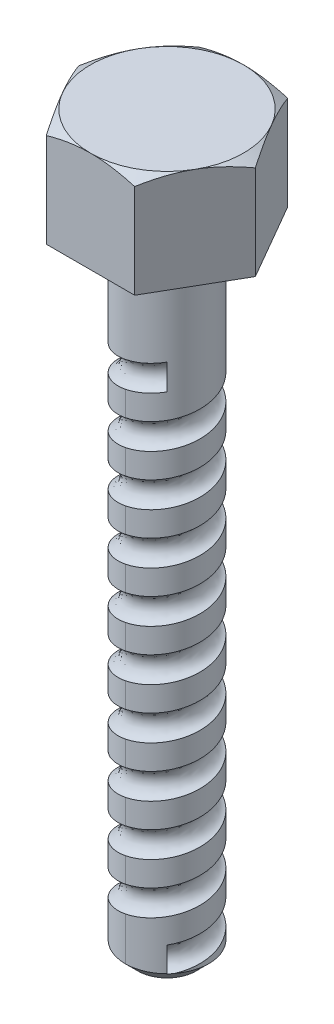
SolidWorks part; units mm, degrees
material "201 Annealed Stainless Steel (SS)"
ref_plane "Front Plane" through (0, 0, 0) normal (0, 0, 1) x (1, 0, 0)
ref_plane "Top Plane" through (0, 0, 0) normal (0, 1, 0) x (1, 0, 0)
ref_plane "Right Plane" through (0, 0, 0) normal (1, 0, 0) x (0, 0, -1)
sketch "Sketch1" plane through (0, 0, 0) normal (0, 1, 0) x (1, 0, 0)
  line L1 (-7, 0) -> (-3.5, -6.0622)
  line L2 (-3.5, -6.0622) -> (3.5, -6.0622)
  line L3 (3.5, -6.0622) -> (7, 0)
  line L4 (7, 0) -> (3.5, 6.0622)
  line L5 (3.5, 6.0622) -> (-3.5, 6.0622)
  line L6 (-3.5, 6.0622) -> (-7, 0)
  circle A0 centre (0, 0) radius 6.0622 construction
  dimension "D1" = 14
extrude "Boss-Extrude1" add sketch "Sketch1" along normal blind 8
sketch "Sketch2" plane through (0, 8, 0) normal (0, 1, 0) x (1, 0, 0)
  line L0 (3.5, 6.0622) -> (-3.5, 6.0622) construction
  circle A0 centre (0, 0) radius 6.0622
extrude "Cut-Extrude2" cut sketch "Sketch2" against normal blind 8 draft 60 flip side to cut
sketch "Sketch3" plane through (0, 0, 0) normal (0, -1, 0) x (1, 0, 0)
  circle A0 centre (0, 0) radius 3.3
  dimension "D1" = 6.6
extrude "Boss-Extrude2" add sketch "Sketch3" along normal blind 50
fillet "Fillet1" radius 1 1 edges at (0, 0, 3.3)
chamfer "Chamfer1" distance 1 angle 45 1 edges at (0, -50, -3.3)
sketch "Sketch4" plane through (0, -50, 0) normal (0, -1, 0) x (1, 0, 0)
  circle A0 centre (0, 0) radius 3.3 construction
  circle A1 centre (0, 0) radius 3.3
curve "Helix/Spiral1" pitch 4 height 40 turns 10
sketch "Sketch5" plane through (0, 0, 0) normal (1, 0, 0) x (0, 0, -1)
  line L0 (-4.5062, -23.0552) -> (-3.2967, -23.5318)
  line L1 (-3.2967, -25.5786) -> (-4.5062, -26.0552)
  line L2 (-4.5062, -23.0552) -> (-4.5062, -26.0552)
  line L3 (-3.7, -24.5552) -> (-4.5062, -24.5552) construction
  line L4 (0, -49) -> (0, -1) construction
  arc A0 (-3.2967, -23.5318) -> (-3.2967, -25.5786) centre (-3.7, -24.5552) cw
  dimension "D1" = 3.7
  dimension "D4" = 1.1
  dimension "D2" = 3
  dimension "D3" = 1.3
  dimension "D5" = 24.5552
sweep "Cut-Sweep1" cut profiles "Sketch5" path "Helix/Spiral1"
scale "Scale1" [suppressed]
equation "\"L\"= 50"
equation "\"D1@Boss-Extrude2\"=\"L\""
